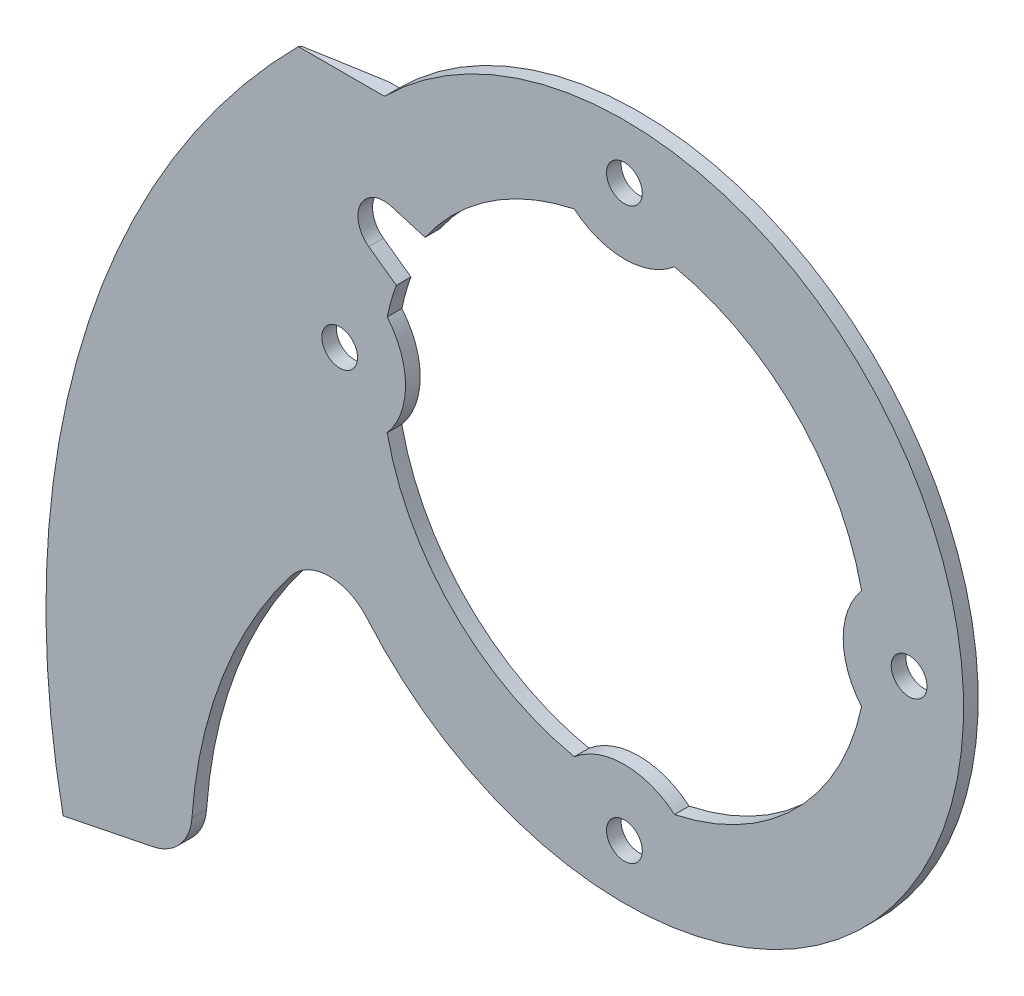
SolidWorks part; units mm, degrees
ref_plane "Plane1" through (0, 0, 0) normal (0, 0, 1) x (1, 0, 0)
ref_plane "Plane2" through (0, 0, 0) normal (0, 1, 0) x (1, 0, 0)
ref_plane "Plane3" through (0, 0, 0) normal (1, 0, 0) x (0, 0, -1)
other "Configuration Table"
sketch "top blade profile" plane through (0, 0, 0) normal (0, 0, 1) x (1, 0, 0)
  line L2 (-15.7137, 6.2585) -> (-14.0211, 5.0417)
  line L3 (-12.2523, 8.4789) -> (-14.3262, 9.092)
  line L4 (-15.7137, 6.2585) -> (-14.0211, 5.0417)
  line L5 (-12.2523, 8.4789) -> (-14.3262, 9.092)
  line L12 (0, 0) -> (-30, 30) construction
  line L13 (0, 0) -> (-24.3334, -14.5781) construction
  line L14 (-14.7432, 14.7432) -> (-20.0432, 14.7432)
  line L15 (-34.4973, -33.4353) -> (-26.6559, -31.8505)
  line L16 (-20.0432, 14.7432) -> (-34.4973, -33.4353) construction
  line L17 (-34.4973, -33.4353) -> (-30.4881, -53.2721) construction
  arc A0 (2.0589, -20.7481) -> (3.4672, 20.5597) centre (0, 0) ccw construction
  arc A1 (-2.0589, 20.7481) -> (-3.4672, -20.5597) centre (0, 0) ccw construction
  arc A2 (-3.4672, -20.5597) -> (3.4672, 20.5597) centre (0, 0) ccw
  arc A3 (3.4672, 20.5597) -> (-14.7432, 14.7432) centre (0, 0) ccw
  arc A4 (-20.0432, 14.7432) -> (-34.4973, -33.4353) centre (17.7955, -22.8664) ccw
  arc A5 (-26.6559, -31.8505) -> (-17.8858, -10.7154) centre (2.814, -31.6919) cw
  arc A8 (-17.8858, -10.7154) -> (-3.4672, -20.5597) centre (0, 0) ccw
  circle A9 centre (-17.5, 0) radius 1.1
  arc A10 (14.5781, 3.0805) -> (3.0805, 14.5781) centre (0, 0) ccw
  arc A11 (14.5781, 3.0805) -> (14.5781, -3.0805) centre (18.22, 0) ccw
  arc A12 (3.0805, -14.5781) -> (14.5781, -3.0805) centre (0, 0) ccw
  arc A13 (3.0805, -14.5781) -> (-3.0805, -14.5781) centre (0, -18.22) ccw
  arc A14 (-14.5781, -3.0805) -> (-3.0805, -14.5781) centre (0, 0) ccw
  arc A15 (-14.5781, -3.0805) -> (-14.5781, 3.0805) centre (-18.22, 0) ccw
  arc A16 (-14.0211, 5.0417) -> (-14.5781, 3.0805) centre (0, 0) ccw
  arc A17 (-14.3262, 9.092) -> (-15.7137, 6.2585) centre (-14.7798, 7.5577) ccw
  arc A18 (-3.0805, 14.5781) -> (-12.2523, 8.4789) centre (0, 0) ccw
  arc A19 (-3.0805, 14.5781) -> (3.0805, 14.5781) centre (0, 18.22) ccw
  arc A20 (14.5781, 3.0805) -> (3.0805, 14.5781) centre (0, 0) ccw
  arc A21 (14.5781, 3.0805) -> (14.5781, -3.0805) centre (18.22, 0) ccw
  arc A22 (3.0805, -14.5781) -> (14.5781, -3.0805) centre (0, 0) ccw
  arc A23 (3.0805, -14.5781) -> (-3.0805, -14.5781) centre (0, -18.22) ccw
  arc A24 (-14.5781, -3.0805) -> (-3.0805, -14.5781) centre (0, 0) ccw
  arc A25 (-14.5781, -3.0805) -> (-14.5781, 3.0805) centre (-18.22, 0) ccw
  arc A26 (-14.0211, 5.0417) -> (-14.5781, 3.0805) centre (0, 0) ccw
  arc A27 (-14.3262, 9.092) -> (-15.7137, 6.2585) centre (-14.7798, 7.5577) ccw
  arc A28 (-3.0805, 14.5781) -> (-12.2523, 8.4789) centre (0, 0) ccw
  arc A29 (-3.0805, 14.5781) -> (3.0805, 14.5781) centre (0, 18.22) ccw
  circle A30 centre (-17.5, 0) radius 1.1
  circle A31 centre (0, -17.5) radius 1.1
  circle A32 centre (0, -17.5) radius 1.1
  circle A33 centre (17.5, 0) radius 1.1
  circle A34 centre (17.5, 0) radius 1.1
  circle A35 centre (0, 17.5) radius 1.1
  circle A36 centre (0, 17.5) radius 1.1
  dimension "D6" = 5.3
  dimension "D7" = 50.3
  dimension "D8" = 38
  dimension "D9" = 8
  dimension "D1" = 0.6
  dimension "D2" = 0.1
  dimension "D3" = 0.1
  dimension "D4" = 0.1
  dimension "D5" = 0.1
extrude "basic blade shape" add sketch "top blade profile" along normal blind 0.9
sketch "grind path" plane through (0, 0, 0.9) normal (0, 0, 1) x (1, 0, 0)
  arc A0 (-20.0432, 14.7432) -> (-34.4973, -33.4353) centre (17.7955, -22.8664) ccw construction
  arc A1 (-14.282, 19.7631) -> (-34.4973, -33.4353) centre (17.7955, -22.8664) ccw
sketch "Sketch1" plane through (5.1386, -25.4245, 0) normal (0.1981, -0.9802, 0) x (0.9802, 0.1981, 0)
  line L0 (-40.4373, 0) -> (-40.4373, 0.8)
  line L1 (-40.4373, 0.9) -> (-40.4373, 0) construction
  line L2 (-40.4373, 0.8) -> (-37.2373, 0)
  line L3 (-40.4373, 0) -> (-32.4373, 0) construction
  line L4 (-37.2373, 0) -> (-40.4373, 0)
  dimension "D1" = 0.1
  dimension "D2" = 3.2
sweep "blade grind" cut profiles "Sketch1" path "grind path"
chamfer "edge grind" distance 0.072 angle 45 2 edges at (-33.3045, -7.5357, 0.8)
fillet "blade root fillet" radius 3 1 edges at (-17.8858, -10.7154, 0.45)
fillet "blade end fillet" radius 3 1 edges at (-26.6559, -31.8505, 0.45)
